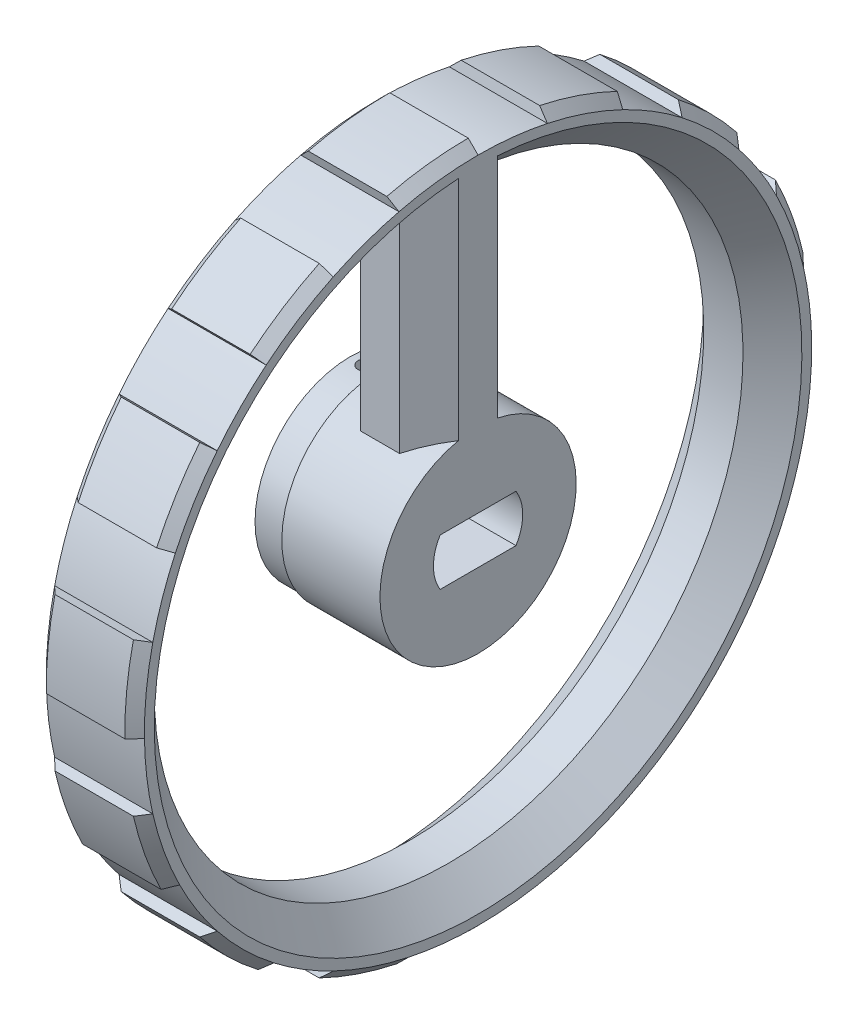
SolidWorks part; units mm, degrees
ref_plane "Front Plane" through (0, 0, 0) normal (0, 0, 1) x (1, 0, 0)
ref_plane "Top Plane" through (0, 0, 0) normal (0, 1, 0) x (1, 0, 0)
ref_plane "Right Plane" through (0, 0, 0) normal (1, 0, 0) x (0, 0, -1)
sketch "Sketch1" plane through (0, 0, 0) normal (1, 0, 0) x (0, 0, -1)
  line L0 (0, 10) -> (0, 30) construction
  line L1 (0, 20) -> (5, 20) construction
  line L2 (0, 20) -> (-5, 20) construction
  line L3 (-5, 29.5804) -> (-5, 8.6603)
  line L4 (5, 29.5804) -> (5, 8.6603)
  circle A0 centre (0, 0) radius 35
  arc A1 (-5, 29.5804) -> (5, 29.5804) centre (0, 0) ccw
  arc A2 (-5, 8.6603) -> (5, 8.6603) centre (0, 0) ccw
  dimension "D1" = 5
  dimension "D2" = 5
extrude "Boss-Extrude1" add sketch "Sketch1" along normal blind 10
chamfer "Chamfer1" distance 1 angle 45 2 edges at (0, 0, -35) (10, 0, -35)
sketch "Sketch2" plane through (10, 0, 0) normal (1, 0, 0) x (0, 0, -1)
  line L0 (0, 0) -> (0, 17.5792) construction
  line L1 (0, 35) -> (0, 34)
  line L2 (7.2769, 34.2352) -> (7.069, 33.257)
  line L3 (0, 34) -> (0, 35) construction
  line L4 (15.1859, 31.5339) -> (14.752, 30.6329)
  line L5 (21.4104, 27.6875) -> (20.7986, 26.8964)
  line L6 (27.3641, 21.8221) -> (26.5823, 21.1987)
  line L7 (31.3032, 15.656) -> (30.4088, 15.2086)
  line L8 (34.1225, 7.7882) -> (33.1475, 7.5657)
  line L9 (34.9961, 0.5236) -> (33.9962, 0.5086)
  line L10 (34.1225, -7.7882) -> (33.1475, -7.5657)
  line L11 (31.7576, -14.7125) -> (30.8502, -14.2921)
  line L12 (27.3641, -21.8221) -> (26.5823, -21.1987)
  line L13 (22.2291, -27.0346) -> (21.5939, -26.2622)
  line L14 (15.1859, -31.5339) -> (14.752, -30.6329)
  line L15 (8.2978, -34.0022) -> (8.0607, -33.0307)
  line L16 (0, -35) -> (0, -34)
  line L17 (-7.2769, -34.2352) -> (-7.069, -33.257)
  line L18 (-15.1859, -31.5339) -> (-14.752, -30.6329)
  line L19 (-21.4104, -27.6875) -> (-20.7986, -26.8964)
  line L20 (-27.3641, -21.8221) -> (-26.5823, -21.1987)
  line L21 (-31.3032, -15.656) -> (-30.4088, -15.2086)
  line L22 (-34.1225, -7.7882) -> (-33.1475, -7.5657)
  line L23 (-34.9961, -0.5236) -> (-33.9962, -0.5086)
  line L24 (-34.1225, 7.7882) -> (-33.1475, 7.5657)
  line L25 (-31.7576, 14.7125) -> (-30.8502, 14.2921)
  line L26 (-27.3641, 21.8221) -> (-26.5823, 21.1987)
  line L27 (-22.2291, 27.0346) -> (-21.5939, 26.2622)
  line L28 (-15.1859, 31.5339) -> (-14.752, 30.6329)
  line L29 (-8.2978, 34.0022) -> (-8.0607, 33.0307)
  circle A0 centre (0, 0) radius 35 construction
  arc A1 (0, 35) -> (7.2769, 34.2352) centre (0, 0) cw
  arc A2 (0, 34) -> (7.069, 33.257) centre (0, 0) cw
  circle A3 centre (0, 0) radius 34 construction
  arc A4 (14.752, 30.6329) -> (20.7986, 26.8964) centre (0, 0) cw
  arc A5 (15.1859, 31.5339) -> (21.4104, 27.6875) centre (0, 0) cw
  arc A6 (26.5823, 21.1987) -> (30.4088, 15.2086) centre (0, 0) cw
  arc A7 (27.3641, 21.8221) -> (31.3032, 15.656) centre (0, 0) cw
  arc A8 (33.1475, 7.5657) -> (33.9962, 0.5086) centre (0, 0) cw
  arc A9 (34.1225, 7.7882) -> (34.9961, 0.5236) centre (0, 0) cw
  arc A10 (33.1475, -7.5657) -> (30.8502, -14.2921) centre (0, 0) cw
  arc A11 (34.1225, -7.7882) -> (31.7576, -14.7125) centre (0, 0) cw
  arc A12 (26.5823, -21.1987) -> (21.5939, -26.2622) centre (0, 0) cw
  arc A13 (27.3641, -21.8221) -> (22.2291, -27.0346) centre (0, 0) cw
  arc A14 (14.752, -30.6329) -> (8.0607, -33.0307) centre (0, 0) cw
  arc A15 (15.1859, -31.5339) -> (8.2978, -34.0022) centre (0, 0) cw
  arc A16 (0, -34) -> (-7.069, -33.257) centre (0, 0) cw
  arc A17 (0, -35) -> (-7.2769, -34.2352) centre (0, 0) cw
  arc A18 (-14.752, -30.6329) -> (-20.7986, -26.8964) centre (0, 0) cw
  arc A19 (-15.1859, -31.5339) -> (-21.4104, -27.6875) centre (0, 0) cw
  arc A20 (-26.5823, -21.1987) -> (-30.4088, -15.2086) centre (0, 0) cw
  arc A21 (-27.3641, -21.8221) -> (-31.3032, -15.656) centre (0, 0) cw
  arc A22 (-33.1475, -7.5657) -> (-33.9962, -0.5086) centre (0, 0) cw
  arc A23 (-34.1225, -7.7882) -> (-34.9961, -0.5236) centre (0, 0) cw
  arc A24 (-33.1475, 7.5657) -> (-30.8502, 14.2921) centre (0, 0) cw
  arc A25 (-34.1225, 7.7882) -> (-31.7576, 14.7125) centre (0, 0) cw
  arc A26 (-26.5823, 21.1987) -> (-21.5939, 26.2622) centre (0, 0) cw
  arc A27 (-27.3641, 21.8221) -> (-22.2291, 27.0346) centre (0, 0) cw
  arc A28 (-14.752, 30.6329) -> (-8.0607, 33.0307) centre (0, 0) cw
  arc A29 (-15.1859, 31.5339) -> (-8.2978, 34.0022) centre (0, 0) cw
  point P68 (0, 0)
  dimension "D1" = 14
extrude "Cut-Extrude1" cut sketch "Sketch2" against normal through all
sketch "Sketch3" plane through (0, 0, 0) normal (-1, 0, 0) x (0, 0, 1)
  circle A0 centre (0, 0) radius 1.5
extrude "Cut-Extrude2" cut sketch "Sketch3" against normal through all
sketch "Sketch4" plane through (0, 0, 0) normal (-1, 0, 0) x (0, 0, 1)
  line L0 (-3.7239, -2.15) -> (3.7239, -2.15) construction
  line L1 (3.7239, 2.15) -> (-3.7239, 2.15) construction
  line L2 (-3.8656, -2.4) -> (3.8656, -2.4)
  line L3 (3.8656, 2.4) -> (-3.8656, 2.4)
  arc A0 (3.7239, -2.15) -> (3.7239, 2.15) centre (0, 0) ccw construction
  arc A1 (-3.7239, 2.15) -> (-3.7239, -2.15) centre (0, 0) ccw construction
  arc A2 (3.8656, -2.4) -> (3.8656, 2.4) centre (0, 0) ccw
  arc A3 (-3.8656, 2.4) -> (-3.8656, -2.4) centre (0, 0) ccw
  dimension "D1" = 0.25
extrude "Cut-Extrude3" cut sketch "Sketch4" against normal blind 10
sketch "Sketch5" plane through (0, 0, 0) normal (-1, 0, 0) x (0, 0, 1)
  line L0 (-3.8656, 2.4) -> (3.8656, 2.4)
  line L1 (-3.8656, -2.4) -> (3.8656, -2.4)
  circle A0 centre (0, 0) radius 9.729
  arc A1 (-3.8656, 2.4) -> (-3.8656, -2.4) centre (-0.1182, 0) ccw
  arc A2 (3.8656, 2.4) -> (3.8656, -2.4) centre (0.1182, 0) cw
extrude "Boss-Extrude2" add sketch "Sketch5" along normal blind 3
sketch "Sketch6" plane through (0, 0, 0) normal (0, 1, 0) x (1, 0, 0)
  line L0 (-3, 0) -> (0, 0) construction
  line L1 (-3, 9.729) -> (-3, -9.729) construction
  circle A0 centre (-1.5, 0) radius 0.75
extrude "Cut-Extrude4" cut sketch "Sketch6" against normal through all both and the other way through all
sketch "Sketch7" plane through (0, 0, 0) normal (-1, 0, 0) x (0, 0, 1)
  line L0 (-7.069, 33.257) -> (0, 0) construction
  line L1 (0, 0) -> (0, 34) construction
  line L2 (-3.554, 33.8137) -> (-3.3449, 31.8247) construction
  line L3 (11.4692, 32.0071) -> (10.8933, 30.0888) construction
  line L4 (-3.3449, 31.8247) -> (-3.1359, 29.8357)
  line L5 (10.8933, 30.0888) -> (10.2125, 28.2083)
  line L6 (10.2125, 28.2083) -> (0, 0) construction
  line L7 (22.796, 22.4575) -> (21.3713, 21.0539)
  line L8 (30.3162, 10.2434) -> (28.4215, 9.6031)
  line L9 (31.7711, -3.8206) -> (29.7854, -3.5818)
  line L10 (26.9104, -17.3156) -> (25.2285, -16.2333)
  line L11 (16.8219, -27.2218) -> (15.7705, -25.5204)
  line L12 (3.2405, -31.8355) -> (3.038, -29.8458)
  line L13 (-10.7946, -30.1244) -> (-10.1199, -28.2416)
  line L14 (-22.8696, -22.3827) -> (-21.4402, -20.9837)
  line L15 (-30.2825, -10.3427) -> (-28.3898, -9.6963)
  line L16 (-31.7584, 3.9248) -> (-29.7735, 3.6795)
  line L17 (-26.9671, 17.2272) -> (-25.2816, 16.1505)
  line L18 (-16.7325, 27.2768) -> (-15.6867, 25.572)
  arc A0 (0, 34) -> (-7.069, 33.257) centre (0, 0) ccw construction
  arc A1 (-3.3449, 31.8247) -> (10.8933, 30.0888) centre (0, 0) cw
  arc A2 (14.752, 30.6329) -> (8.0607, 33.0307) centre (0, 0) ccw construction
  arc A3 (-3.1359, 29.8357) -> (10.2125, 28.2083) centre (0, 0) cw
  arc A4 (21.3713, 21.0539) -> (28.4215, 9.6031) centre (0, 0) cw
  arc A5 (22.796, 22.4575) -> (30.3162, 10.2434) centre (0, 0) cw
  arc A6 (29.7854, -3.5818) -> (25.2285, -16.2333) centre (0, 0) cw
  arc A7 (31.7711, -3.8206) -> (26.9104, -17.3156) centre (0, 0) cw
  arc A8 (15.7705, -25.5204) -> (3.038, -29.8458) centre (0, 0) cw
  arc A9 (16.8219, -27.2218) -> (3.2405, -31.8355) centre (0, 0) cw
  arc A10 (-10.1199, -28.2416) -> (-21.4402, -20.9837) centre (0, 0) cw
  arc A11 (-10.7946, -30.1244) -> (-22.8696, -22.3827) centre (0, 0) cw
  arc A12 (-28.3898, -9.6963) -> (-29.7735, 3.6795) centre (0, 0) cw
  arc A13 (-30.2825, -10.3427) -> (-31.7584, 3.9248) centre (0, 0) cw
  arc A14 (-25.2816, 16.1505) -> (-15.6867, 25.572) centre (0, 0) cw
  arc A15 (-26.9671, 17.2272) -> (-16.7325, 27.2768) centre (0, 0) cw
  point P44 (0, 0)
  dimension "D1" = 7
sketch "Sketch8" plane through (0, 0, 0) normal (-1, 0, 0) x (0, 0, 1)
  line L0 (0, 9.729) -> (0, 36.6659) construction
  line L1 (-9.729, 0) -> (-40.9988, 0) construction
  line L2 (9.729, 0) -> (42.9555, 0) construction
  line L3 (0, -9.729) -> (0, -38.8091) construction
  line L4 (6.8795, 6.8795) -> (25.8887, 25.8887) construction
  circle A3 centre (0, 0) radius 9.729 construction
  circle A4 centre (0, 0) radius 9.729 construction
  arc A5 (0, 9.729) -> (9.729, 0) centre (0, 0) cw construction
  circle A6 centre (-11.3137, -11.3137) radius 2
  circle A7 centre (11.3137, -11.3137) radius 2
  circle A8 centre (11.3137, 11.3137) radius 2
  circle A9 centre (-11.3137, 11.3137) radius 2
  dimension "D1" = 16
chamfer "Chamfer2" distance 3 angle 45 6 edges at (10, 19.1203, -5) (10, -30, 0) (10, 19.1203, 5) (0, 19.1203, 5) (0, -30, 0) (0, 19.1203, -5)
